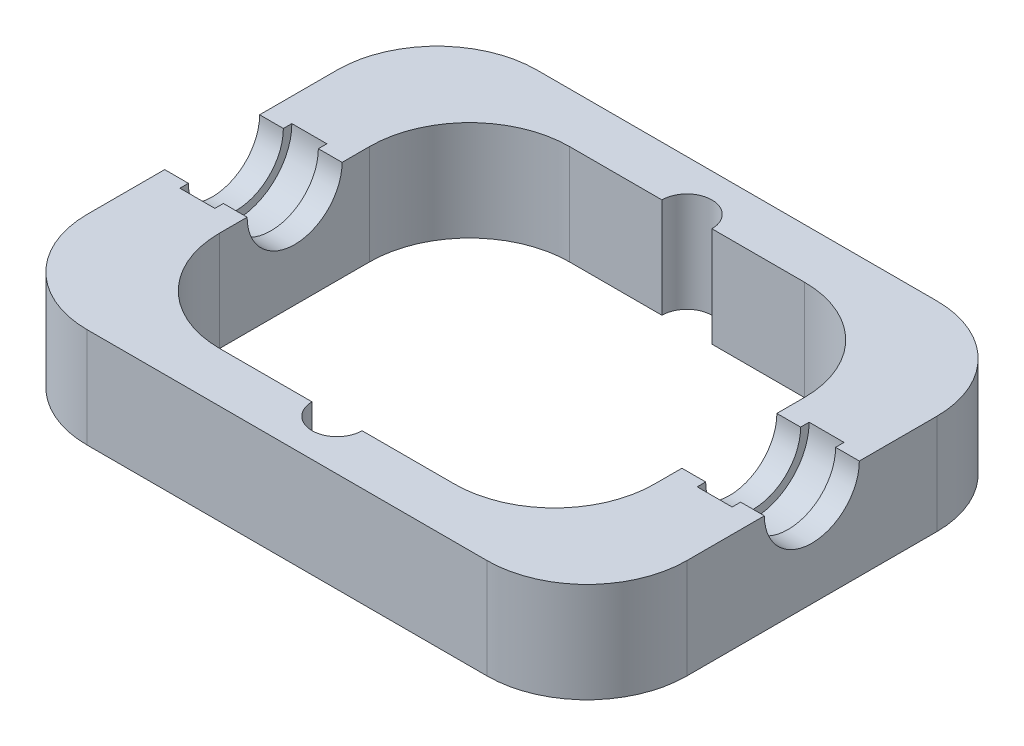
SolidWorks part; units mm, degrees
ref_plane "Спереди" through (0, 0, 0) normal (0, 0, 1) x (1, 0, 0)
ref_plane "Сверху" through (0, 0, 0) normal (0, 1, 0) x (1, 0, 0)
ref_plane "Справа" through (0, 0, 0) normal (1, 0, 0) x (0, 0, -1)
sketch "Sketch2" plane through (0, 0, 0) normal (0, 1, 0) x (1, 0, 0)
  line L1 (60, -45) -> (-60, -45)
  line L2 (60, -45) -> (60, 45)
  line L3 (60, 45) -> (-60, 45)
  line L4 (-60, -45) -> (-60, 45)
  line L5 (60, -45) -> (-60, 45) construction
  line L6 (60, 45) -> (-60, -45) construction
  line L7 (43.5, -35) -> (-43.5, -35)
  line L8 (43.5, -35) -> (43.5, 35)
  line L9 (43.5, 35) -> (-43.5, 35)
  line L10 (-43.5, -35) -> (-43.5, 35)
  line L11 (43.5, -35) -> (-43.5, 35) construction
  line L12 (43.5, 35) -> (-43.5, -35) construction
  point P0 (0, 0)
  point P6 (0, 0)
  dimension "D1" = 120
  dimension "D2" = 87
  dimension "D3" = 70
  dimension "D4" = 90
extrude "Boss-Extrude1" add sketch "Sketch2" along normal blind 20
sketch "Sketch3" plane through (0, 20, 0) normal (0, 1, 0) x (1, 0, 0)
  line L0 (-43.5, 0) -> (-60, 0) construction
  line L2 (-48.25, 11.2) -> (-55.25, 11.2)
  line L3 (-43.5, 35) -> (-43.5, -35) construction
  line L4 (-60, 45) -> (-60, -45) construction
  line L5 (43.5, 0) -> (60, 0) construction
  line L6 (43.5, -35) -> (43.5, 35) construction
  line L7 (60, -45) -> (60, 45) construction
  line L8 (51.75, 0) -> (51.75, 45) construction
  line L9 (60, 45) -> (-60, 45) construction
  line L10 (-51.75, 0) -> (-51.75, 45) construction
  line L11 (-48.25, 11.2) -> (-48.25, 0)
  line L12 (-48.25, 0) -> (-55.25, 0)
  line L13 (-55.25, 11.2) -> (-55.25, 0)
  line L14 (-48.25, 11.2) -> (-55.25, 0) construction
  line L15 (-48.25, 0) -> (-55.25, 11.2) construction
  line L16 (55.25, 11.2) -> (48.25, 11.2)
  line L17 (55.25, 11.2) -> (55.25, 0)
  line L18 (55.25, 0) -> (48.25, 0)
  line L19 (48.25, 11.2) -> (48.25, 0)
  line L20 (55.25, 11.2) -> (48.25, 0) construction
  line L21 (55.25, 0) -> (48.25, 11.2) construction
  point P18 (-51.75, 5.6)
  point P23 (51.75, 5.6)
  dimension "D1" = 7
  dimension "D2" = 11.2
revolve "Cut-Revolve1" cut sketch "Sketch3" angle 360 about L18
sketch "Sketch4" plane through (60, 0, 0) normal (1, 0, 0) x (0, 0, -1)
  line L0 (-45, 20) -> (45, 20) construction
  circle A0 centre (0, 20) radius 9.5
  dimension "D1" = 19
extrude "Cut-Extrude1" cut sketch "Sketch4" against normal through all
fillet "Fillet1" radius 20 8 edges at (60, 10, -45) (60, 10, 45) (-60, 10, -45) (-60, 10, 45) (43.5, 10, -35) (43.5, 10, 35) (-43.5, 10, 35) (-43.5, 10, -35)
sketch "Sketch5" plane through (0, 20, 0) normal (0, 1, 0) x (1, 0, 0)
  line L0 (-23.5, -35) -> (23.5, -35) construction
  line L1 (23.5, 35) -> (-23.5, 35) construction
  circle A0 centre (0, -35) radius 5
  circle A1 centre (0, 35) radius 5
  dimension "D1" = 10
extrude "Cut-Extrude2" cut sketch "Sketch5" against normal through all
